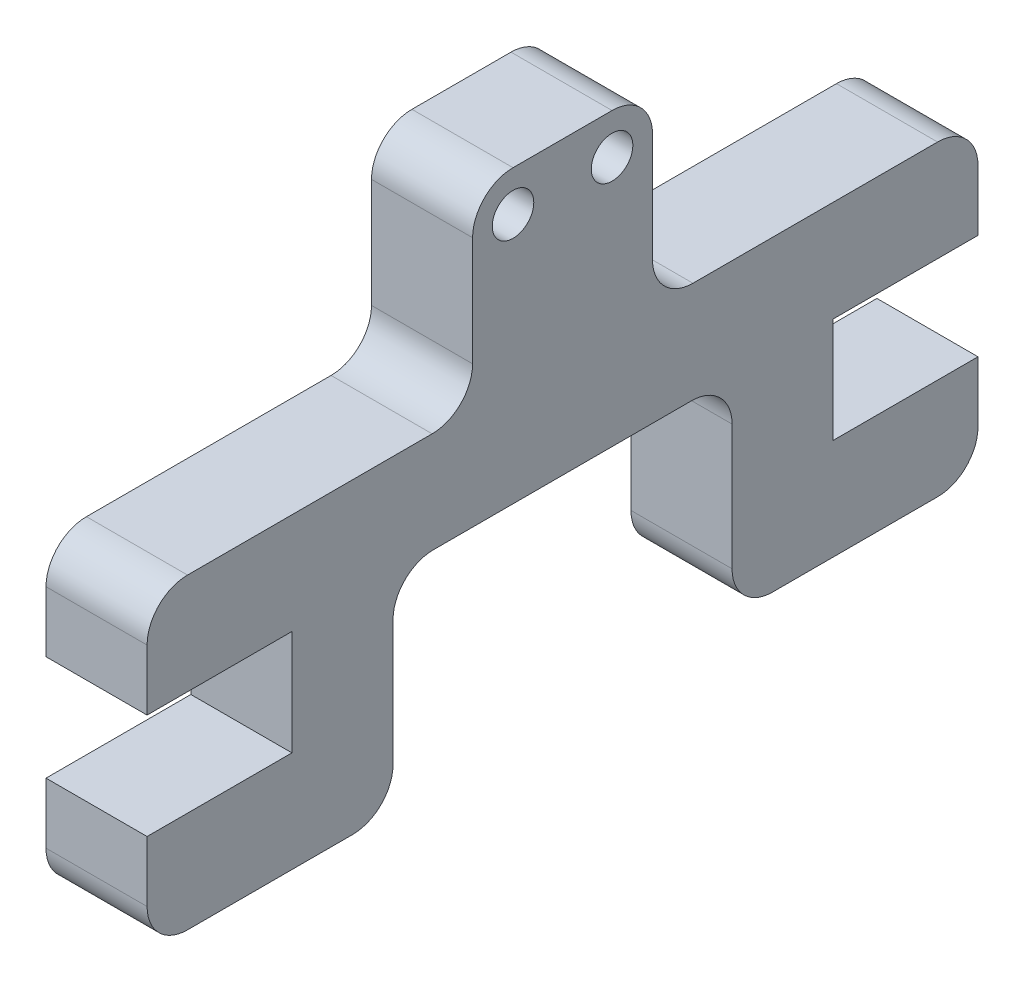
SolidWorks part; units mm, degrees
ref_plane "Front Plane" through (0, 0, 0) normal (0, 0, 1) x (1, 0, 0)
ref_plane "Top Plane" through (0, 0, 0) normal (0, 1, 0) x (1, 0, 0)
ref_plane "Right Plane" through (0, 0, 0) normal (1, 0, 0) x (0, 0, -1)
sketch "Sketch1" plane through (0, 0, 0) normal (1, 0, 0) x (0, 0, -1)
  line L0 (17.8, -18.8) -> (50, -18.8)
  line L1 (0, 0) -> (17.8, 0)
  line L4 (17.8, 0) -> (17.8, -18.8)
  line L9 (-32.2, -28.8) -> (50, -28.8)
  line L10 (50, -28.8) -> (50, -18.8)
  line L11 (0, 0) -> (0, -18.8)
  line L12 (0, -18.8) -> (-32.2, -18.8)
  line L13 (-32.2, -18.8) -> (-32.2, -28.8)
  dimension "D1" = 17.8
  dimension "D2" = 18.8
  dimension "D3" = 10
  dimension "D4" = 32.2
extrude "Boss-Extrude1" add sketch "Sketch1" along normal blind 10
sketch "Sketch3" plane through (10, 0, 0) normal (1, 0, 0) x (0, 0, -1)
  line L0 (0, -4) -> (17.8, -4) construction
  line L2 (17.8, -18.8) -> (17.8, 0) construction
  line L3 (17.8, 0) -> (0, 0) construction
  line L4 (0, 0) -> (0, -18.8) construction
  circle A0 centre (4, -4) radius 2.055
  circle A1 centre (13.8, -4) radius 2.055
  dimension "D4" = 4.11
  dimension "D1" = 4
  dimension "D2" = 4
  dimension "D3" = 4
extrude "Cut-Extrude1" cut sketch "Sketch3" against normal through all
sketch "Sketch4" plane through (10, 0, 0) normal (1, 0, 0) x (0, 0, -1)
  line L0 (-17.87, -28.8) -> (-17.87, -39.2)
  line L1 (-32.2, -28.8) -> (50, -28.8) construction
  line L2 (-17.87, -39.2) -> (-32.2, -39.2)
  line L3 (-32.2, -39.2) -> (-32.2, -49.2)
  line L4 (-32.2, -49.2) -> (-7.87, -49.2)
  line L5 (-7.87, -49.2) -> (-7.87, -28.8)
  line L6 (-17.87, -28.8) -> (-7.87, -28.8)
  line L7 (-32.2, -18.8) -> (-32.2, -28.8) construction
  line L8 (8.9, 0) -> (8.9, -28.8) construction
  line L9 (17.8, 0) -> (0, 0) construction
  line L16 (0, 0) -> (0, -18.8) construction
  line L17 (35.67, -28.8) -> (25.67, -28.8)
  line L18 (25.67, -49.2) -> (25.67, -28.8)
  line L19 (50, -49.2) -> (25.67, -49.2)
  line L20 (50, -39.2) -> (50, -49.2)
  line L21 (35.67, -39.2) -> (50, -39.2)
  line L22 (35.67, -28.8) -> (35.67, -39.2)
  point P8 (-5.3465, -28.8)
  point P11 (-3.9287, -28.8)
  point P21 (0, -28.8)
  dimension "D1" = 10
  dimension "D2" = 10.4
  dimension "D3" = 7.87
extrude "Boss-Extrude2" add sketch "Sketch4" against normal up to surface (10 mm away) up to face at (0, -4, -6.055)
fillet "Fillet1" radius 4 2 edges at (5, 0, -17.8) (5, 0, 0)
fillet "Fillet2" radius 4 10 edges at (5, -49.2, -50) (5, -49.2, -25.67) (5, -28.8, -25.67) (5, -28.8, 7.87) (5, -49.2, 7.87) (5, -49.2, 32.2) (5, -18.8, -50) (5, -18.8, 32.2) (5, -18.8, -17.8) (5, -18.8, 0)
